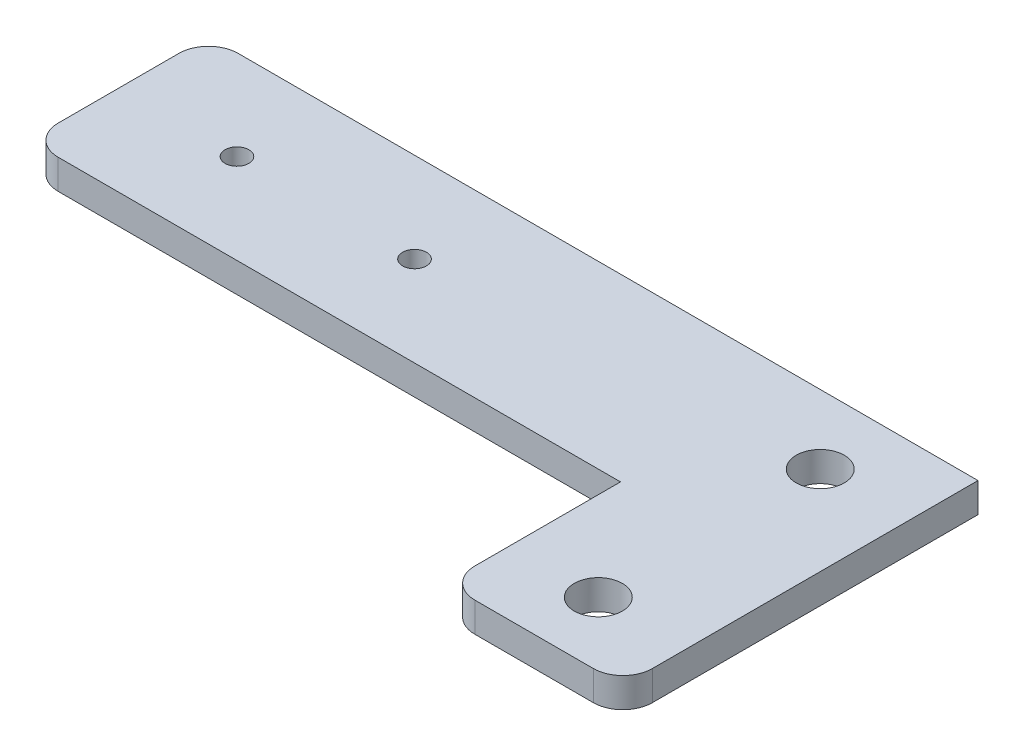
SolidWorks part; units mm, degrees
ref_plane "Front Plane" through (0, 0, 0) normal (0, 0, 1) x (1, 0, 0)
ref_plane "Top Plane" through (0, 0, 0) normal (0, 1, 0) x (1, 0, 0)
ref_plane "Right Plane" through (0, 0, 0) normal (1, 0, 0) x (0, 0, -1)
sketch "Sketch3" plane through (0, 0, 0) normal (0, 1, 0) x (1, 0, 0)
  line L0 (0, 0) -> (165.1, 0)
  line L3 (165.1, 0) -> (165.1, -76.2)
  line L4 (165.1, -76.2) -> (127, -76.2)
  line L5 (127, -76.2) -> (127, -38.608)
  line L6 (127, -38.608) -> (0, -38.608)
  line L7 (0, -38.608) -> (0, 0)
  dimension "D1" = 76.2
  dimension "D2" = 127
  dimension "D3" = 38.608
  dimension "D4" = 38.1
extrude "Boss-Extrude1" add sketch "Sketch3" along normal blind 6.35
sketch "Sketch4" plane through (0, 6.35, 0) normal (0, 1, 0) x (1, 0, 0)
  line L0 (127, -76.2) -> (165.1, -76.2) construction
  line L1 (127, -38.608) -> (127, -76.2) construction
  line L2 (0, 0) -> (0, -38.608) construction
  line L3 (127, -76.2) -> (165.1, -76.2) construction
  line L4 (88.9, 0) -> (88.9, -38.608) construction
  line L5 (165.1, 0) -> (0, 0) construction
  line L6 (0, -38.608) -> (127, -38.608) construction
  line L7 (165.1, -76.2) -> (165.1, 0) construction
  line L8 (165.1, 0) -> (0, 0) construction
  line L9 (146.05, -14.7955) -> (146.05, -62.4205) construction
  line L10 (127, 0) -> (127, -76.2) construction
  line L11 (25.4, -19.304) -> (63.5, -19.304) construction
  line L12 (0, -38.608) -> (88.9, -38.608) construction
  circle A0 centre (25.4, -19.304) radius 2.5527
  circle A1 centre (63.5, -19.304) radius 2.5527
  circle A4 centre (146.05, -14.7955) radius 5.1562
  circle A5 centre (146.05, -62.4205) radius 5.1562
  point P8 (146.05, -76.2)
  point P16 (0, -19.304)
  point P29 (146.05, -38.608)
  point P32 (44.45, -38.608)
  point P34 (44.45, -19.304)
  dimension "D1" = 5.1054
  dimension "D2" = 10.3124
  dimension "D3" = 47.625
  dimension "D4" = 88.9
  dimension "D5" = 76.2
  dimension "D6" = 38.1
extrude "Cut-Extrude1" cut sketch "Sketch4" against normal up to next
fillet "Fillet1" radius 6.35 4 edges at (165.1, 3.175, 76.2) (127, 3.175, 76.2) (0, 3.175, 38.608) (0, 3.175, 0)
